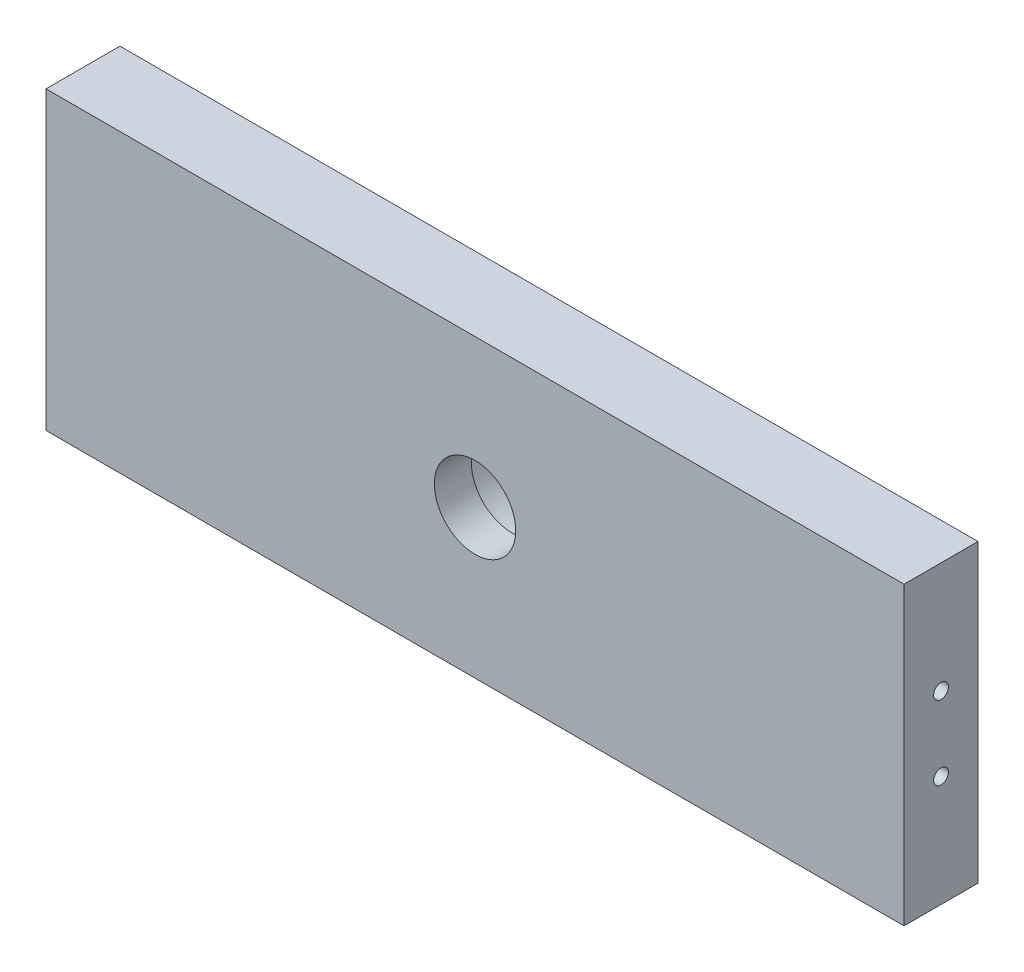
SolidWorks part; units mm, degrees
ref_plane "Front Plane" through (0, 0, 0) normal (0, 0, 1) x (1, 0, 0)
ref_plane "Top Plane" through (0, 0, 0) normal (0, 1, 0) x (1, 0, 0)
ref_plane "Right Plane" through (0, 0, 0) normal (1, 0, 0) x (0, 0, -1)
sketch "Sketch1" plane through (0, 0, 0) normal (0, 0, 1) x (1, 0, 0)
  line L1 (-58, 20) -> (58, 20)
  line L2 (-58, 20) -> (-58, -20)
  line L3 (-58, -20) -> (58, -20)
  line L4 (58, 20) -> (58, -20)
  line L5 (-58, 20) -> (58, -20) construction
  line L6 (-58, -20) -> (58, 20) construction
  circle A0 centre (0, 0) radius 5.5
  point P0 (0, 0)
  dimension "D3" = 11
  dimension "D1" = 40
  dimension "D2" = 116
extrude "Boss-Extrude2" add sketch "Sketch1" along normal blind 10
ref_plane "Plane1" through (58, 0, 0) normal (1, 0, 0) x (0, 0, -1)
sketch "Sketch4" plane through (58, 0, 0) normal (1, 0, 0) x (0, 0, -1)
  line L0 (-10, 0) -> (0, 0)
  line L1 (-10, 20) -> (-10, -20) construction
  circle A0 centre (-5, 5) radius 1
  circle A1 centre (-5, -5) radius 1
  dimension "D1" = 2
  dimension "D2" = 5
  dimension "D3" = 5
extrude "Cut-Extrude1" cut sketch "Sketch4" against normal blind 10 contours A1 | A0
ref_plane "Plane2" through (58, 0, 0) normal (1, 0, 0) x (0, 0, -1)
ref_plane "Plane3" through (-58, 0, 0) normal (-1, 0, 0) x (0, 0, 1)
sketch "Sketch6" plane through (-58, 0, 0) normal (-1, 0, 0) x (0, 0, 1)
  line L0 (0, 0) -> (10, 0)
  line L1 (10, 20) -> (10, -20) construction
  circle A0 centre (5, 5) radius 1
  circle A1 centre (5, -5) radius 1
  dimension "D1" = 2
  dimension "D2" = 5
  dimension "D3" = 5
extrude "Cut-Extrude3" cut sketch "Sketch6" against normal blind 10 contours A0 | A1
ref_plane "Plane4" through (-58, 0, 0) normal (-1, 0, 0) x (0, 0, 1)
ref_plane "Plane5" through (0, 0, 0) normal (0, 0, 1) x (1, 0, 0)
sketch "Sketch8" plane through (0, 0, 0) normal (0, 0, 1) x (1, 0, 0)
  circle A0 centre (0, 0) radius 8.05
  dimension "D1" = 16.1
extrude "Cut-Extrude8" cut sketch "Sketch8" along normal blind 5
